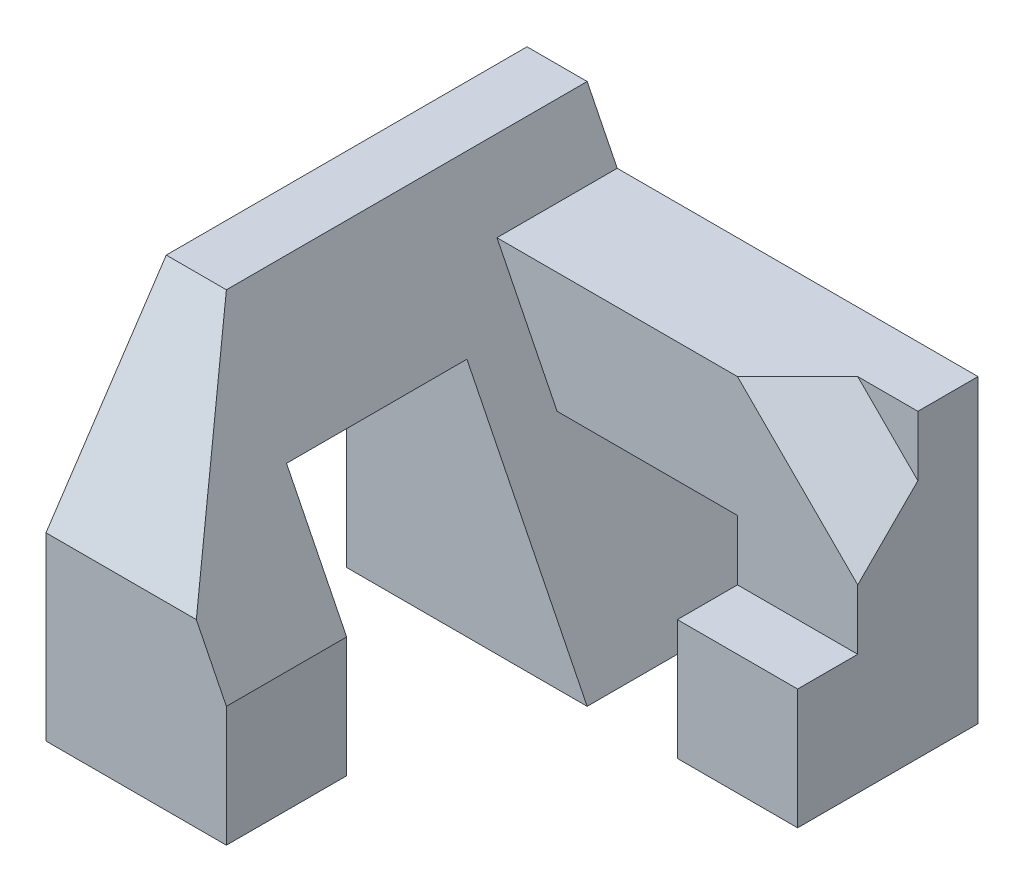
SolidWorks part; units mm, degrees
ref_plane "Front Plane" through (0, 0, 0) normal (0, 0, 1) x (1, 0, 0)
ref_plane "Top Plane" through (0, 0, 0) normal (0, 1, 0) x (1, 0, 0)
ref_plane "Right Plane" through (0, 0, 0) normal (1, 0, 0) x (0, 0, -1)
sketch "Sketch1" plane through (0, 0, 0) normal (0, 0, 1) x (1, 0, 0)
  line L1 (2, -3) -> (-2, -3)
  line L2 (2, -3) -> (2, 3)
  line L3 (2, 3) -> (-2, 3)
  line L4 (-2, -3) -> (-2, 3)
  line L5 (2, -3) -> (-2, 3) construction
  line L6 (2, 3) -> (-2, -3) construction
  point P0 (0, 0)
  dimension "D1" = 4
  dimension "D2" = 6
extrude "Boss-Extrude1" add sketch "Sketch1" along normal blind 8
sketch "Sketch2" plane through (0, 3, 0) normal (0, 1, 0) x (1, 0, 0)
  line L0 (-1, 0) -> (-1, -5)
  line L1 (2, 0) -> (-2, 0) construction
  line L2 (-1, -5) -> (0, -5)
  line L3 (0, -5) -> (0, 0)
  line L4 (0, 0) -> (-1, 0)
  line L5 (2, -8) -> (2, 0) construction
  dimension "D1" = 1
  dimension "D2" = 2
  dimension "D3" = 5
ref_plane "Plane2" through (0.4, 0.2, 0) normal (0.8944, 0.4472, 0) x (0, 0, -1)
sketch "Sketch6" plane through (0.4, 0.2, 0) normal (0.8944, 0.4472, 0) x (0, 0, -1)
  line L0 (0, 3.1305) -> (-8, 3.1305)
  line L1 (-8, 3.1305) -> (-8, -3.5777)
  line L2 (-8, -3.5777) -> (0, -3.5777)
  line L3 (0, -3.5777) -> (0, 3.1305)
  line L4 (-8, 1.7889) -> (-8, 3.5777) construction
extrude "Cut-Extrude4" cut sketch "Sketch6" along normal blind 8
sketch "Sketch7" plane through (-2, 0, 0) normal (-1, 0, 0) x (0, 0, 1)
  line L0 (3, -3) -> (3, 0)
  line L1 (3, 0) -> (6, 0)
  line L2 (6, 0) -> (6, -3)
  line L3 (6, -3) -> (3, -3)
  line L4 (8, -3) -> (0, -3) construction
  dimension "D1" = 3
  dimension "D2" = 2
extrude "Cut-Extrude5" cut sketch "Sketch7" against normal through all
sketch "Sketch8" plane through (0, -3, 0) normal (0, -1, 0) x (1, 0, 0)
  line L0 (2, 8) -> (1, 8)
  line L1 (-2, 8) -> (2, 8) construction
  line L2 (1, 8) -> (1, 6)
  line L3 (2, 6) -> (-2, 6) construction
  line L4 (1, 6) -> (2, 6)
  line L5 (2, 6) -> (2, 8)
  dimension "D1" = 1
extrude "Cut-Extrude6" cut sketch "Sketch8" against normal through all
sketch "Sketch9" plane through (-2, 0, 0) normal (-1, 0, 0) x (0, 0, 1)
  line L0 (3, 0) -> (3, 1)
  line L1 (3, 1) -> (6, 1)
  line L2 (6, 1) -> (6, 0)
  line L3 (6, 0) -> (3, 0)
  dimension "D1" = 1
extrude "Cut-Extrude7" cut sketch "Sketch9" against normal through all
sketch "Sketch10" plane through (-2, 0, 0) normal (-1, 0, 0) x (0, 0, 1)
  line L0 (6, 3) -> (8, 0)
  line L1 (8, 3) -> (0, 3) construction
  line L2 (8, 3) -> (8, -3) construction
  line L3 (8, 0) -> (8, 3)
  line L4 (8, 3) -> (6, 3)
  dimension "D1" = 2
  dimension "D2" = 3
extrude "Cut-Extrude8" cut sketch "Sketch10" against normal through all
sketch "Sketch12" plane through (1, 0, 0) normal (1, 0, 0) x (0, 0, -1)
  line L0 (0, 2) -> (0, 0)
  line L1 (0, 0) -> (-2, 0)
  line L2 (-2, 0) -> (-2, 2)
  line L3 (0, 2) -> (-2, 2)
  line L4 (-3, -3) -> (-3, 1) construction
  line L5 (0, 3) -> (-6, 3) construction
  dimension "D1" = 2
  dimension "D2" = 2
  dimension "D3" = 1
  dimension "D4" = 1
extrude "Boss-Extrude2" add sketch "Sketch12" along normal mid plane 6
sketch "Sketch13" plane through (4, 0, 0) normal (1, 0, 0) x (0, 0, -1)
  line L0 (0, 2) -> (-2, 2)
  line L1 (-2, 2) -> (-2, 0)
  line L2 (-2, 0) -> (0, 0)
  line L3 (0, 0) -> (0, 2)
extrude "Boss-Extrude3" add sketch "Sketch13" along normal blind 1.5
sketch "Sketch14" plane through (0, 0, 0) normal (0, -1, 0) x (1, 0, 0)
  line L0 (5.5, 2) -> (3.5, 2)
  line L1 (5.5, 2) -> (0.5, 2) construction
  line L2 (3.5, 2) -> (3.5, 0)
  line L3 (5.5, 0) -> (0.5, 0) construction
  line L4 (3.5, 0) -> (5.5, 0)
  line L5 (5.5, 0) -> (5.5, 2)
  dimension "D1" = 2
extrude "Boss-Extrude4" add sketch "Sketch14" along normal blind 3
sketch "Sketch15" plane through (0, 0, 2) normal (0, 0, 1) x (1, 0, 0)
  line L0 (5.5, -3) -> (5.5, -1)
  line L1 (5.5, 2) -> (5.5, -3) construction
  line L2 (5.5, -1) -> (3.5, -1)
  line L3 (3.5, -3) -> (3.5, 0) construction
  line L4 (3.5, -1) -> (3.5, -3)
  line L5 (3.5, -3) -> (5.5, -3)
  dimension "D1" = 2
extrude "Boss-Extrude5" add sketch "Sketch15" along normal blind 1
sketch "Sketch16" plane through (0, 0, 2) normal (0, 0, 1) x (1, 0, 0)
  line L0 (3.5, 2) -> (5.5, 0)
  line L1 (5.5, 2) -> (-0.5, 2) construction
  line L2 (5.5, 2) -> (5.5, -1) construction
  line L3 (5.5, 0) -> (5.5, 2)
  line L4 (5.5, 2) -> (3.5, 2)
  dimension "D1" = 2
  dimension "D2" = 2
sketch "Sketch17" plane through (0, 2, 0) normal (0, 1, 0) x (1, 0, 0)
  line L0 (5.5, 0) -> (5.5, -2) construction
  line L1 (5.5, 0) -> (-0.5, 0) construction
  point P0 (4.5, -1)
  dimension "D1" = 1
  dimension "D2" = 1
ref_plane "Plane3" through (2.5, 2.5, 2.5) normal (0.5774, 0.5774, 0.5774) x (0.8165, -0.4082, -0.4082)
sketch "Sketch18" plane through (0, 0, 2) normal (0, 0, 1) x (1, 0, 0)
  line L0 (5.5, 1) -> (4.5, 2)
  line L1 (5.5, 2) -> (5.5, -1) construction
  line L2 (4.5, 2) -> (5.5, 2)
  line L3 (5.5, 2) -> (5.5, 1)
  dimension "D1" = 1
extrude "Cut-Extrude9" cut sketch "Sketch18" against normal blind 1
sketch "Sketch19" plane through (0, 2, 0) normal (0, 1, 0) x (1, 0, 0)
  line L0 (4.5, -2) -> (-0.5, -2) construction
  point P0 (3.5, -2)
  dimension "D1" = 1
sketch "Sketch20" plane through (5.5, 0, 0) normal (1, 0, 0) x (0, 0, -1)
  line L0 (-2, 1) -> (-2, -1) construction
  point P0 (-2, 0)
  dimension "D1" = 1
sketch3d "3DSketch1"
  line L0 (5.5, 0, 2) -> (5.5, 1, 1)
  line L1 (5.5, 1, 1) -> (4.5, 2, 1)
  line L2 (4.5, 2, 1) -> (3.5, 2, 2)
  line L3 (3.5, 2, 2) -> (5.5, 0, 2)
extrude "Cut-Extrude10" cut sketch "3DSketch1" along direction (-0.7071, -0.7071, 0) on the side against the normal blind 1
